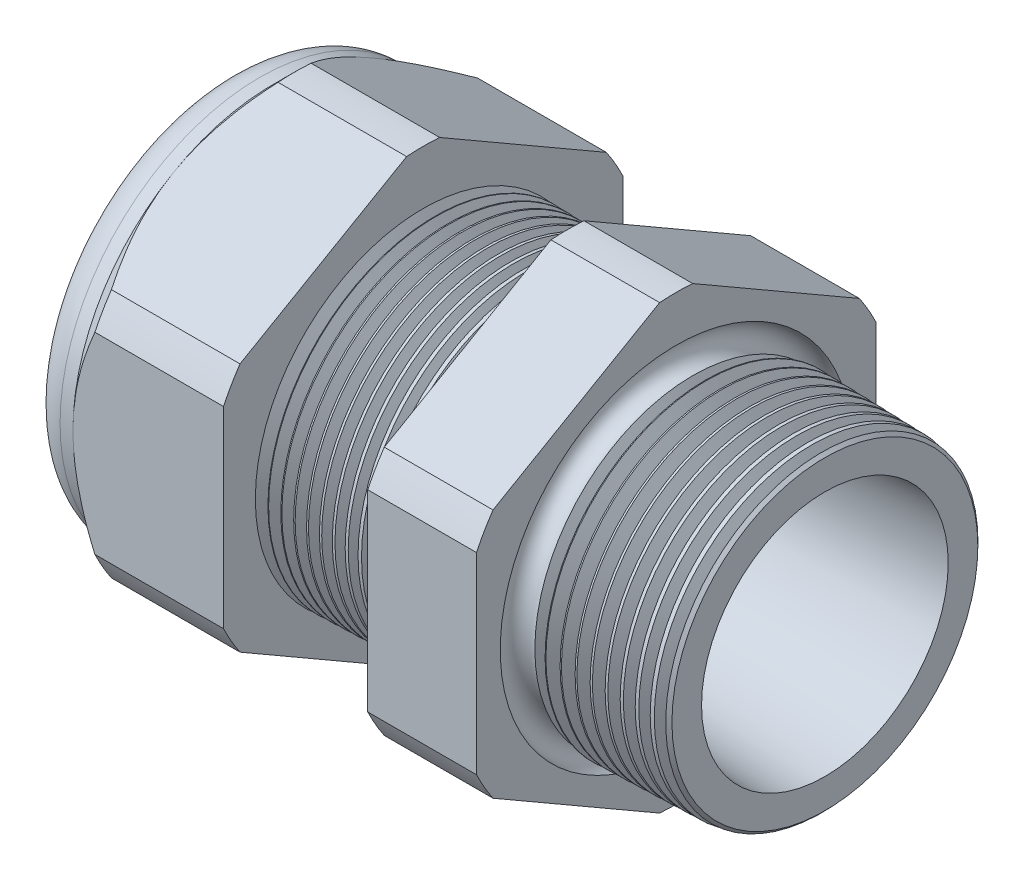
SolidWorks part; units mm, degrees
ref_plane "Front Plane" through (0, 0, 0) normal (0, 0, 1) x (1, 0, 0)
ref_plane "Top Plane" through (0, 0, 0) normal (0, 1, 0) x (1, 0, 0)
ref_plane "Right Plane" through (0, 0, 0) normal (1, 0, 0) x (0, 0, -1)
sketch "Sketch10" plane through (0, 0, 0) normal (0, 0, 1) x (1, 0, 0)
  line L0 (0, 0) -> (-115.3565, 0) construction
  line L1 (-34.798, 5.969) -> (-22.998, 5.969)
  line L2 (1.016, 7.3722) -> (1.016, 9.4042)
  line L3 (-7.874, 9.637) -> (1.016, 9.4042)
  line L4 (-7.874, 23.876) -> (-7.874, 9.637)
  line L5 (-7.874, 23.876) -> (-14.374, 23.876)
  line L6 (-14.374, 23.876) -> (-14.374, 9.8072)
  line L7 (-22.998, 10.033) -> (-14.374, 9.8072)
  line L8 (-22.998, 10.033) -> (-22.998, 23.876)
  line L9 (-22.998, 23.876) -> (-31.998, 23.876)
  line L10 (-31.998, 23.876) -> (-31.998, 11.938)
  line L11 (-31.998, 11.938) -> (-34.798, 11.938)
  line L12 (-34.798, 11.938) -> (-34.798, 5.969)
  line L13 (-22.998, 5.969) -> (1.016, 7.3722)
  dimension "D1" = 35.814
  dimension "D2" = 11.938
  dimension "D3" = 1.5
  dimension "D4" = 2.032
  dimension "A" = 20.066
  dimension "D6" = 23.876
  dimension "D8" = 47.752
  dimension "D9" = 2.8
  dimension "D10" = 9
  dimension "D11" = 6.5
  dimension "D" = 8.89
revolve "Revolve2" add sketch "Sketch10" angle 360 about L0
sketch "Sketch12" plane through (-31.998, 0, 0) normal (-1, 0, 0) x (0, 0, 1)
  line L1 (-0.9882, 13.2143) -> (-10.9498, 7.4629)
  line L2 (-11.938, 5.7513) -> (-11.938, -5.7513)
  line L3 (-10.9498, -7.4629) -> (-0.9882, -13.2143)
  line L4 (0.9882, -13.2143) -> (10.9498, -7.4629)
  line L5 (11.938, -5.7513) -> (11.938, 5.7513)
  line L6 (10.9498, 7.4629) -> (0.9882, 13.2143)
  circle A0 centre (0, 0) radius 11.938 construction
  arc A1 (0.9882, 13.2143) -> (-0.9882, 13.2143) centre (0, 0) ccw
  arc A2 (-10.9498, 7.4629) -> (-11.938, 5.7513) centre (0, 0) ccw
  arc A3 (-11.938, -5.7513) -> (-10.9498, -7.4629) centre (0, 0) ccw
  arc A4 (-0.9882, -13.2143) -> (0.9882, -13.2143) centre (0, 0) ccw
  arc A5 (10.9498, -7.4629) -> (11.938, -5.7513) centre (0, 0) ccw
  arc A6 (11.938, 5.7513) -> (10.9498, 7.4629) centre (0, 0) ccw
  dimension "D2" = 26.5024
  dimension "D1" = 23.876
extrude "Cut-Extrude2" cut sketch "Sketch12" against normal through all flip side to cut
fillet "Fillet4" radius 2.032 1 edges at (-34.798, 0, -11.938)
sketch "Sketch19" plane through (-31.998, 0, 0) normal (-1, 0, 0) x (0, 0, 1)
  line L0 (11.938, 0) -> (11.938, 5.7513) construction
  circle A0 centre (0, 0) radius 11.938
extrude "Cut-Extrude3" cut sketch "Sketch19" against normal blind 2 draft 45 flip side to cut
chamfer "Chamfer1" distance 0.254 angle 45 1 edges at (1.016, 0, -9.4042)
sketch "Sketch21" plane through (-34.798, 0, 0) normal (-1, 0, 0) x (0, 0, 1)
  circle A0 centre (0, 0) radius 5.969
  circle A2 centre (0, 0) radius 5.969 construction
extrude "plug" add sketch "Sketch21" against normal blind 6.35 separate body
sketch "Sketch22" plane through (-34.798, 0, 0) normal (-1, 0, 0) x (0, 0, 1)
  circle A0 centre (0, 0) radius 5.715
  circle A1 centre (0, 0) radius 5.969 construction
  dimension "D1" = 0.254
extrude "Cut-Extrude4" cut sketch "Sketch22" against normal blind 0.508
sketch "Sketch27" plane through (-34.29, 0, 0) normal (-1, 0, 0) x (0, 0, 1)
  line L0 (-4.3624, 0) -> (4.3624, 0) construction
  circle A0 centre (-4.6949, 0) radius 1.016
  circle A1 centre (0, 0) radius 5.715 construction
  dimension "D1" = 0.0041
  dimension "holedia" = 2.032
extrude "plugholes" cut sketch "Sketch27" against normal through all
pattern_circular "CirPattern1" count 3 over 360 about axis through (0, 0, 0) along (1, 0, 0) of "plugholes"
sketch "Sketch28" [suppressed] plane through (-29.464, 0, 0) normal (-1, 0, 0) x (0, 0, 1)
  circle A0 centre (0, 0) radius 0.762
  dimension "midholedia" = 2.032
extrude "midhole" [suppressed] cut sketch "Sketch28" against normal through all
sketch "Sketch29" plane through (0, 0, 0) normal (0, 0, 1) x (1, 0, 0)
  line L0 (-22.998, 10.033) -> (-22.265, 10.0138)
  line L1 (-14.374, 9.8072) -> (-22.998, 10.033) construction
  line L2 (-22.265, 10.0138) -> (-22.6481, 9.3886)
  line L3 (-22.6481, 9.3886) -> (-22.998, 10.033)
  dimension "D1" = 60
  dimension "D2" = 60
  dimension "D3" = 0.635
revolve "Cut-Revolve1" cut sketch "Sketch29" angle 360 about axis through (0, 0, 0) along (-1, 0, 0)
pattern_linear "LPattern1" count 11 spacing 0.762 along (1, 0, 0) of "Cut-Revolve1"
sketch "Sketch30" plane through (0, 0, 0) normal (0, 0, 1) x (1, 0, 0)
  line L0 (-7.874, 9.637) -> (-6.9944, 9.6139)
  line L1 (-7.874, 13.2143) -> (-7.874, 7.4629) construction
  line L2 (0.7621, 9.4108) -> (-7.874, 9.637) construction
  line L3 (-6.9944, 9.6139) -> (-7.4542, 8.8637)
  line L4 (-7.4542, 8.8637) -> (-7.874, 9.637)
  dimension "D1" = 60
  dimension "D2" = 60
  dimension "D3" = 0.762
revolve "Cut-Revolve2" cut sketch "Sketch30" angle 360 about axis through (0, 0, 0) along (-1, 0, 0)
pattern_linear "LPattern2" count 10 spacing 0.889 along (1, 0, 0) of "Cut-Revolve2"
sketch "Sketch31" [suppressed] plane through (-38.354, 0, 0) normal (-1, 0, 0) x (0, 0, 1)
  line L0 (-1.905, 1.905) -> (1.905, 1.905)
  line L1 (-1.905, -1.905) -> (1.905, -1.905)
  circle A0 centre (0, 0) radius 1.905 construction
  arc A1 (-1.905, 1.905) -> (-1.905, -1.905) centre (-1.905, 0) ccw
  arc A2 (1.905, 1.905) -> (1.905, -1.905) centre (1.905, 0) cw
extrude "Cut-Extrude5" [suppressed] cut sketch "Sketch31" against normal through all
sketch "Sketch32" plane through (0, 0, 0) normal (0, 0, 1) x (1, 0, 0)
  line L0 (-7.874, 13.2143) -> (-7.874, 7.4629) construction
  circle A0 centre (-7.747, 9.637) radius 0.889
  dimension "D2" = 1.778
  dimension "D1" = 0.127
revolve "Cut-Revolve3" cut sketch "Sketch32" angle 360 about axis through (0, 0, 0) along (-1, 0, 0)
